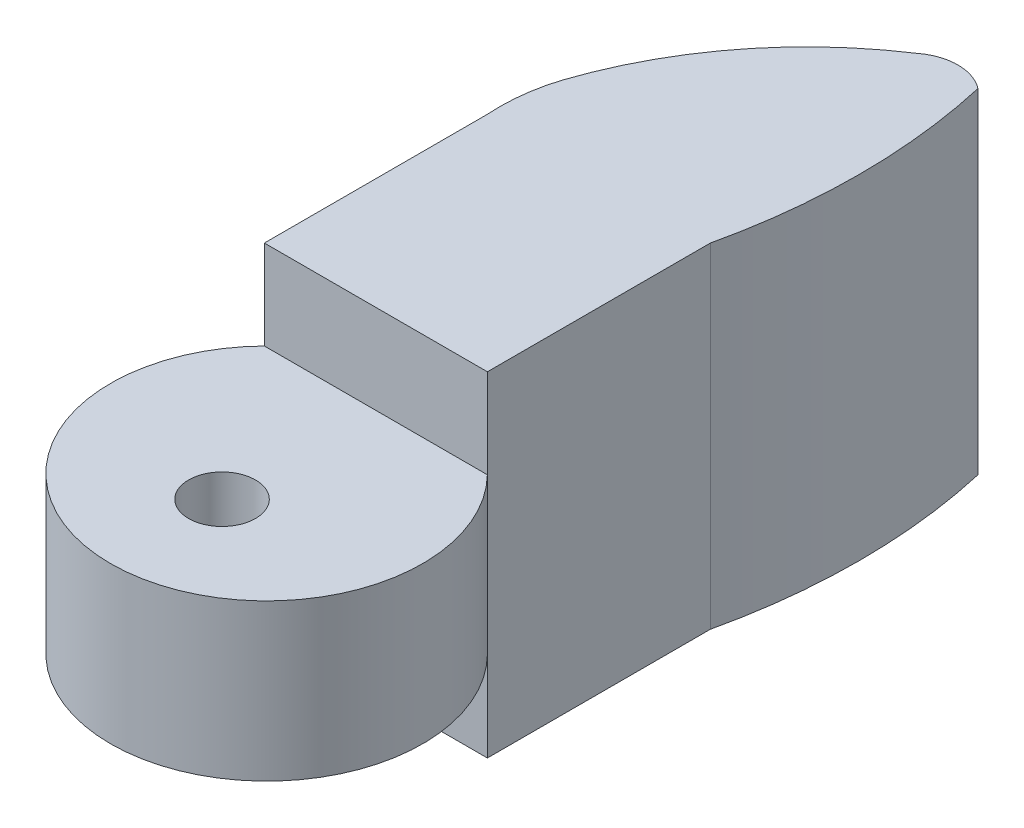
SolidWorks part; units mm, degrees
material "ABS PC"
ref_plane "Front Plane" through (0, 0, 0) normal (0, 0, 1) x (1, 0, 0)
ref_plane "Top Plane" through (0, 0, 0) normal (0, 1, 0) x (1, 0, 0)
ref_plane "Right Plane" through (0, 0, 0) normal (1, 0, 0) x (0, 0, -1)
sketch "Sketch1" plane through (0, 0, 0) normal (0, 0, 1) x (1, 0, 0)
  line L1 (-6.35, -9.525) -> (6.35, -9.525)
  line L2 (-6.35, -9.525) -> (-6.35, 9.525)
  line L3 (-6.35, 9.525) -> (6.35, 9.525)
  line L4 (6.35, -9.525) -> (6.35, 9.525)
  line L5 (-6.35, -9.525) -> (6.35, 9.525) construction
  line L6 (-6.35, 9.525) -> (6.35, -9.525) construction
  point P0 (0, 0)
  dimension "D1" = 19.05
  dimension "D2" = 12.7
extrude "Boss-Extrude1" add sketch "Sketch1" along normal blind 12.7 contours L3 L4 L1 L2
ref_plane "Plane1" through (0, 5.08, 0) normal (0, 1, 0) x (1, 0, 0)
sketch "Sketch5" plane through (0, 5.08, 0) normal (0, 1, 0) x (1, 0, 0)
  line L0 (-6.35, 0) -> (6.35, 0)
  line L1 (-6.35, 0) -> (6.35, 0) construction
  arc A0 (6.35, 0) -> (6.35, 15.24) centre (-27.106, 7.62) ccw
  arc A1 (6.35, 15.24) -> (2.8803, 15.24) centre (4.6152, 12.9892) ccw
  arc A2 (-6.35, 0) -> (-5.9127, 3.7848) centre (4.0448, 0.7168) cw
  arc A3 (2.8803, 15.24) -> (-5.9127, 3.7848) centre (14.97, -3.1425) ccw
  dimension "D1" = 10.4194
  dimension "D2" = 15.24
  dimension "D3" = 3.81
  dimension "D4" = 22.0018
  dimension "D7" = 2.8418
  dimension "D8" = 15.2963
  dimension "D9" = 4.1078
  dimension "D10" = 7.62
  dimension "D5" = 8.7931
  dimension "D6" = 3.4697
extrude "Boss-Extrude3" add sketch "Sketch5" against normal blind 14.605 and the other way blind 4.445 contours L0 A0 A1 A3 A2
sketch "Sketch8" plane through (0, 0, 0) normal (0, 1, 0) x (1, 0, 0)
  line L0 (-6.35, -12.7) -> (6.35, -12.7)
  arc A0 (-6.35, -12.7) -> (6.35, -12.7) centre (0, -18.9217) ccw
  dimension "D1" = 8.89
extrude "Boss-Extrude5" add sketch "Sketch8" along normal mid plane 8.89 contours A0 L0
sketch "Sketch9" plane through (0, 4.445, 0) normal (0, 1, 0) x (1, 0, 0)
  circle A0 centre (0, -21.4617) radius 1.905
  arc A1 (-6.35, -12.7) -> (6.35, -12.7) centre (0, -18.9217) ccw construction
  point P2 (0, -27.8117)
  dimension "D1" = 3.81
  dimension "D2" = 6.35
extrude "Cut-Extrude1" cut sketch "Sketch9" against normal up to surface (8.89 mm away) up to face at (0, -4.445, 20.2559)
